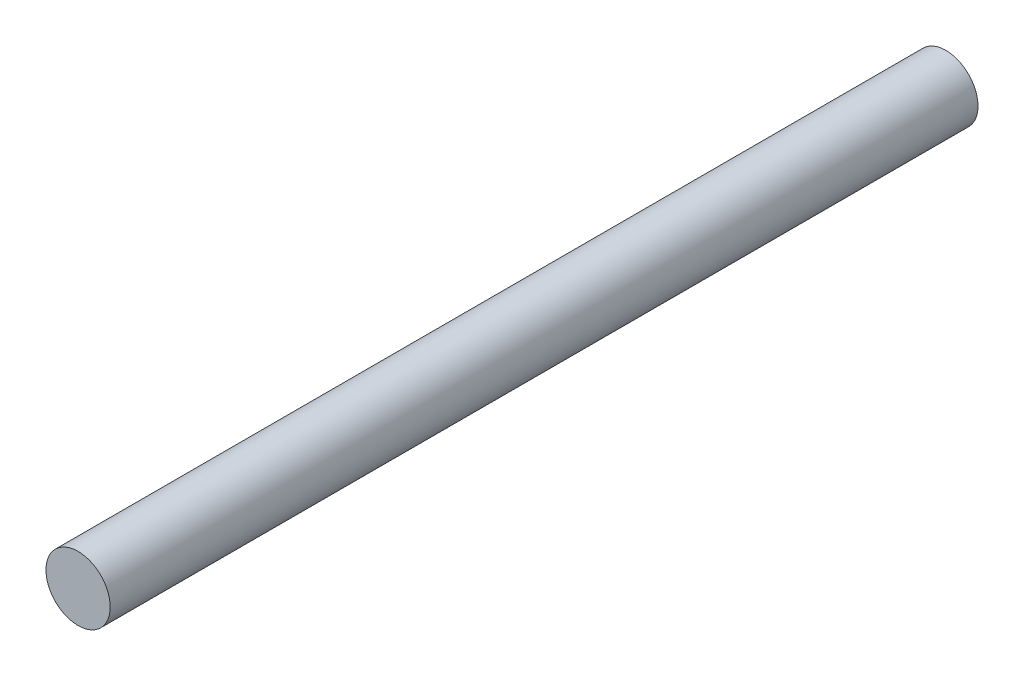
SolidWorks part; units mm, degrees
ref_plane "前视基准面" through (0, 0, 0) normal (0, 0, 1) x (1, 0, 0)
ref_plane "上视基准面" through (0, 0, 0) normal (0, 1, 0) x (1, 0, 0)
ref_plane "右视基准面" through (0, 0, 0) normal (1, 0, 0) x (0, 0, -1)
sketch "草图1" plane through (0, 0, 0) normal (0, 0, 1) x (1, 0, 0)
  circle A0 centre (0, 0) radius 3
  dimension "D1" = 6
extrude "凸台-拉伸1" add sketch "草图1" along normal blind 81
cosmetic thread "装饰螺纹线1" parameters "D1"=8, "D2"=4.917
cosmetic thread "装饰螺纹线2" parameters "D1"=8, "D2"=4.917
